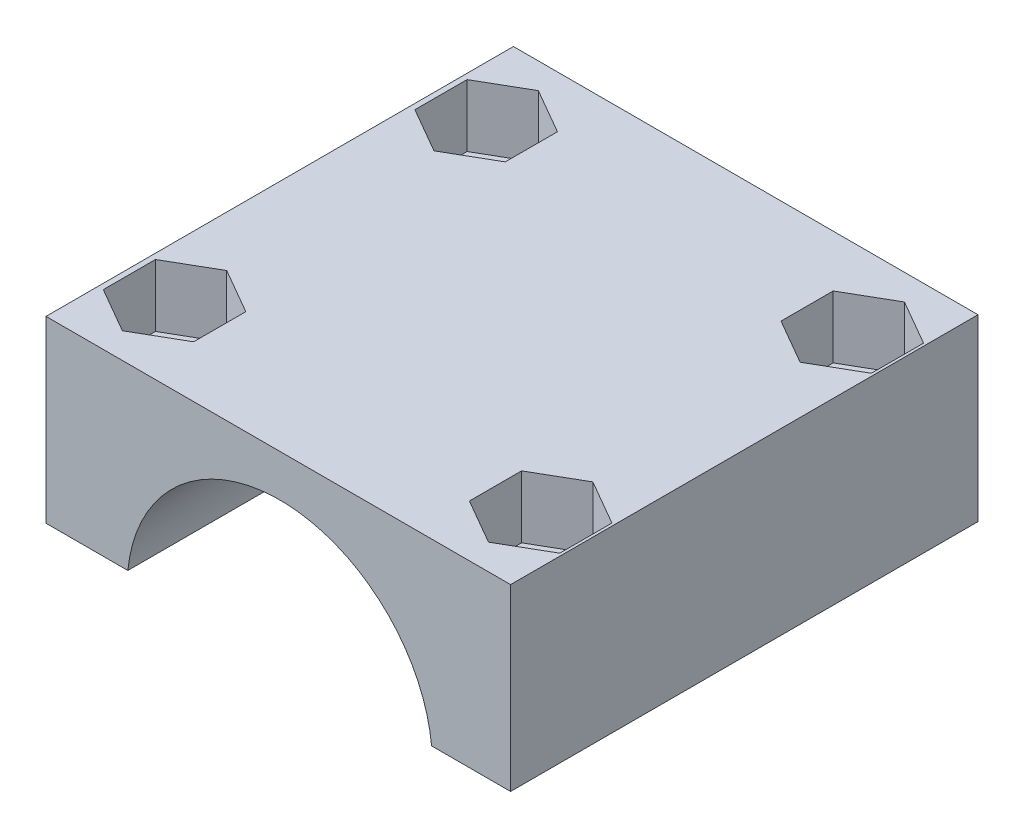
SolidWorks part; units mm, degrees
ref_plane "Ebene vorne" through (0, 0, 0) normal (0, 0, 1) x (1, 0, 0)
ref_plane "Ebene oben" through (0, 0, 0) normal (0, 1, 0) x (1, 0, 0)
ref_plane "Ebene rechts" through (0, 0, 0) normal (1, 0, 0) x (0, 0, -1)
sketch "Skizze1" plane through (0, 0, 0) normal (0, 0, 1) x (1, 0, 0)
  line L0 (-63.5962, 25.8652) -> (-58.345, 25.8652)
  line L1 (-48.5962, 37.3652) -> (-63.5962, 37.3652)
  line L2 (-48.5962, 37.3652) -> (-34.8473, 37.3652)
  line L3 (-63.5962, 25.8652) -> (-63.5962, 37.3652)
  line L4 (-34.8473, 25.8652) -> (-38.8473, 25.8652)
  line L5 (-34.1767, 25.8652) -> (-33.7785, 25.8652)
  line L6 (-34.8473, 25.8652) -> (-34.1767, 25.8652)
  line L8 (-33.7785, 25.8652) -> (-33.7785, 37.3652)
  line L9 (-33.7785, 37.3652) -> (-34.8473, 37.3652)
  arc A0 (-38.8473, 25.8652) -> (-58.345, 25.8652) centre (-48.5962, 24.8652) ccw
extrude "Aufsatz-Linear austragen1" add sketch "Skizze1" against normal blind 30
hole_wizard "Ø3.0 (3) Durchmesser Bohrung1" positions "Skizze3" profile "Skizze2" hole size "Ø3.0" standard "ANSI Metrisch" end condition through all
sketch "Skizze3" plane through (0, 37.3652, 0) normal (0, 1, 0) x (1, 0, 0)
  point P0 (-36.8473, 5)
  point P3 (-60.345, 5)
  point P6 (-60.345, 25)
  point P9 (-36.8473, 25)
sketch "Skizze2" plane through (-36.8473, 37.3652, -5) normal (1, 0, 0) x (0, 0, 1)
  line L0 (0, 0) -> (0, 11.5)
  line L1 (0, 11.5) -> (1.5, 11.5)
  line L2 (1.5, 11.5) -> (1.5, 0)
  line L5 (1.5, 0) -> (0, 0)
  line L11 (0, -6.35) -> (0, 107.95) construction
  dimension "Bohrerdurchmesser" = 3
  dimension "Bohrungstiefe" = 11.5
sketch "Skizze4" plane through (0, 37.3652, 0) normal (0, 1, 0) x (1, 0, 0)
  line L0 (-39.7473, 26.6743) -> (-39.7473, 23.3257)
  line L1 (-60.345, 28.3486) -> (-63.245, 26.6743)
  line L2 (-63.245, 26.6743) -> (-63.245, 23.3257)
  line L3 (-63.245, 23.3257) -> (-60.345, 21.6514)
  line L4 (-60.345, 21.6514) -> (-57.445, 23.3257)
  line L5 (-57.445, 23.3257) -> (-57.445, 26.6743)
  line L6 (-57.445, 26.6743) -> (-60.345, 28.3486)
  line L7 (-36.8473, 21.6514) -> (-33.9473, 23.3257)
  line L8 (-36.8473, 28.3486) -> (-39.7473, 26.6743)
  line L9 (-39.7473, 23.3257) -> (-36.8473, 21.6514)
  line L10 (-33.9473, 26.6743) -> (-36.8473, 28.3486)
  line L11 (-33.9473, 23.3257) -> (-33.9473, 26.6743)
  line L12 (-63.245, 6.6743) -> (-63.245, 3.3257)
  line L13 (-36.8473, 8.3486) -> (-39.7473, 6.6743)
  line L14 (-33.9473, 3.3257) -> (-33.9473, 6.6743)
  line L15 (-39.7473, 6.6743) -> (-39.7473, 3.3257)
  line L16 (-63.245, 3.3257) -> (-60.345, 1.6514)
  line L17 (-39.7473, 3.3257) -> (-36.8473, 1.6514)
  line L18 (-57.445, 6.6743) -> (-60.345, 8.3486)
  line L19 (-60.345, 1.6514) -> (-57.445, 3.3257)
  line L20 (-33.9473, 6.6743) -> (-36.8473, 8.3486)
  line L21 (-60.345, 8.3486) -> (-63.245, 6.6743)
  line L22 (-36.8473, 1.6514) -> (-33.9473, 3.3257)
  line L23 (-57.445, 3.3257) -> (-57.445, 6.6743)
  circle A0 centre (-60.345, 25) radius 2.9 construction
  circle A1 centre (-36.8473, 25) radius 2.9 construction
  circle A2 centre (-60.345, 5) radius 2.9 construction
  circle A3 centre (-36.8473, 5) radius 2.9 construction
extrude "Schnitt-Linear austragen1" cut sketch "Skizze4" against normal blind 4
